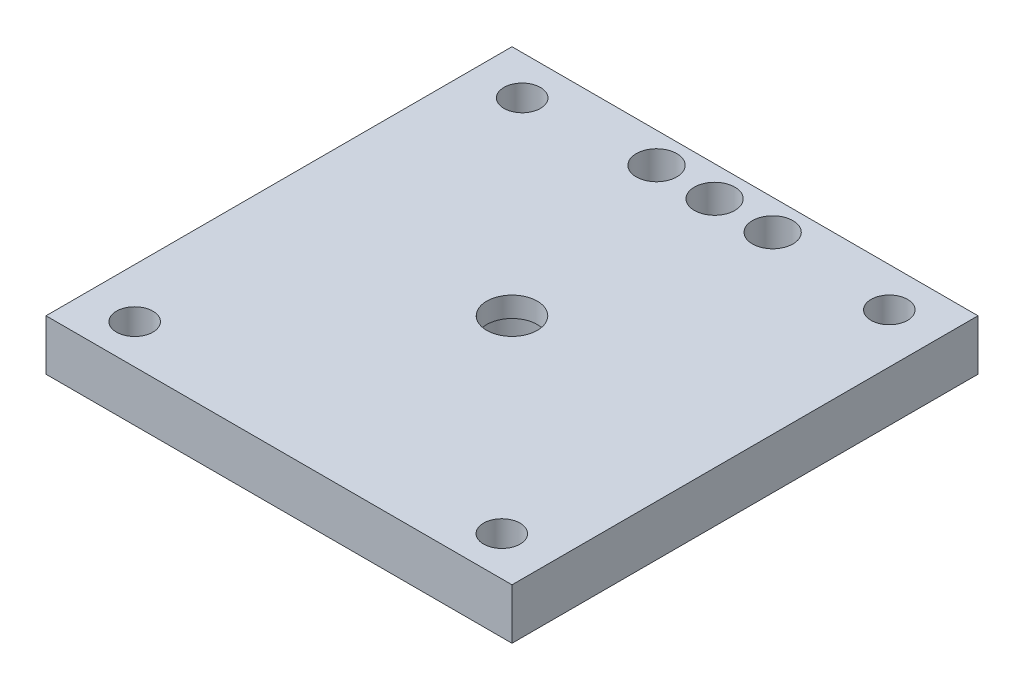
SolidWorks part; units mm, degrees
ref_plane "Front Plane" through (0, 0, 0) normal (0, 0, 1) x (1, 0, 0)
ref_plane "Top Plane" through (0, 0, 0) normal (0, 1, 0) x (1, 0, 0)
ref_plane "Right Plane" through (0, 0, 0) normal (1, 0, 0) x (0, 0, -1)
sketch "Sketch2" plane through (0, 0, 0) normal (0, 1, 0) x (1, 0, 0)
  line L1 (-23, 23) -> (23, 23)
  line L2 (-23, 23) -> (-23, -23)
  line L3 (-23, -23) -> (23, -23)
  line L4 (23, 23) -> (23, -23)
  line L5 (-23, 23) -> (23, -23) construction
  line L6 (-23, -23) -> (23, 23) construction
  point P0 (0, 0)
extrude "Boss-Extrude1" add sketch "Sketch2" along normal blind 5
sketch "Sketch3" plane through (0, 0, 0) normal (0, 1, 0) x (1, 0, 0)
  line L0 (0, 0) -> (-18.12, 0) construction
  line L1 (-18.12, 0) -> (-18.12, 19.125) construction
  line L2 (-18.12, 19.125) -> (18.12, 19.125) construction
  line L3 (18.12, 19.125) -> (18.12, -19.125) construction
  line L4 (18.12, -19.125) -> (-18.12, -19.125) construction
  circle A0 centre (-18.12, 19.125) radius 1.8
  circle A1 centre (18.12, 19.125) radius 1.8
  circle A2 centre (18.12, -19.125) radius 1.8
  circle A3 centre (-18.12, -19.125) radius 1.8
  circle A4 centre (0, 0) radius 2.5
extrude "Cut-Extrude1" cut sketch "Sketch3" along normal blind 5
sketch "Sketch4" plane through (0, 0, 0) normal (0, 1, 0) x (1, 0, 0)
  circle A0 centre (0, 0) radius 4.1
extrude "Cut-Extrude2" cut sketch "Sketch4" along normal blind 3
sketch "Sketch5" plane through (0, 0, 0) normal (0, 1, 0) x (1, 0, 0)
  line L0 (0, 0) -> (0, -4.9397) construction
  line L1 (0, -4.9397) -> (5.8624, -4.9397) construction
  line L2 (0, 0) -> (0, 5.0695) construction
  line L3 (0, 5.0695) -> (-5.733, 5.0695) construction
  line L5 (-3.733, 7.0695) -> (-7.733, 7.0695)
  line L6 (-3.733, 7.0695) -> (-3.733, 3.0695)
  line L7 (-3.733, 3.0695) -> (-7.733, 3.0695)
  line L8 (-7.733, 7.0695) -> (-7.733, 3.0695)
  line L9 (-3.733, 7.0695) -> (-7.733, 3.0695) construction
  line L10 (-3.733, 3.0695) -> (-7.733, 7.0695) construction
  line L11 (3.8624, -2.9397) -> (7.8624, -2.9397)
  line L12 (3.8624, -2.9397) -> (3.8624, -6.9397)
  line L13 (3.8624, -6.9397) -> (7.8624, -6.9397)
  line L14 (7.8624, -2.9397) -> (7.8624, -6.9397)
  line L15 (3.8624, -2.9397) -> (7.8624, -6.9397) construction
  line L16 (3.8624, -6.9397) -> (7.8624, -2.9397) construction
extrude "Boss-Extrude2" add sketch "Sketch5" against normal blind 3
ref_plane "Plane1" through (0, -3, 0) normal (0, -1, 0) x (-1, 0, 0)
ref_plane "Plane2" through (0, 5, 0) normal (0, 1, 0) x (1, 0, 0)
sketch "Sketch9" plane through (0, 0, 0) normal (0, 1, 0) x (1, 0, 0)
  line L0 (-5.733, 23) -> (-5.733, 20) construction
  line L1 (23, 23) -> (-23, 23) construction
  line L2 (5.73, 23) -> (5.73, 20) construction
  line L3 (-5.733, 23) -> (0, 23) construction
  line L4 (0, 23) -> (5.73, 23) construction
  circle A0 centre (-5.733, 20) radius 2
  circle A1 centre (5.73, 20) radius 2
  circle A2 centre (0, 20) radius 2
extrude "Cut-Extrude6" cut sketch "Sketch9" along normal through all
